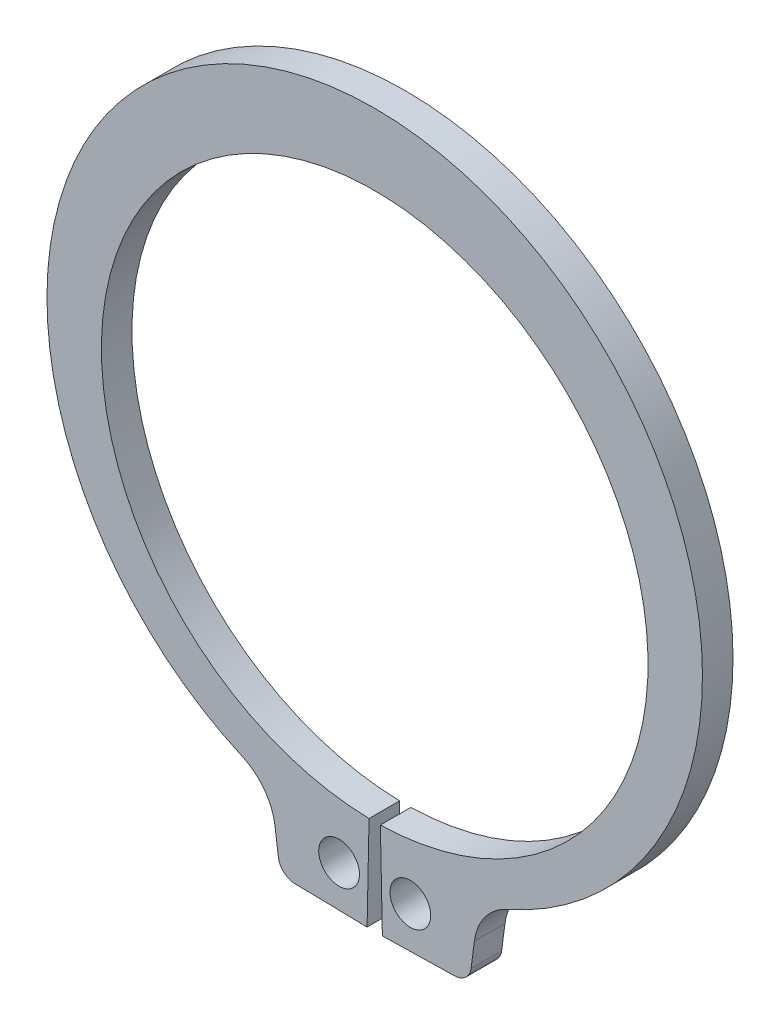
SolidWorks part; units mm, degrees
ref_plane "Plane1" through (0, 0, 0) normal (0, 0, 1) x (1, 0, 0)
ref_plane "Plane2" through (0, 0, 0) normal (0, 1, 0) x (1, 0, 0)
ref_plane "Plane3" through (0, 0, 0) normal (1, 0, 0) x (0, 0, -1)
sketch "Clipboard" plane through (0, 0, 0) normal (0, 0, 1) x (1, 0, 0)
  line L0 (0, 0) -> (2.1, 0)
  line L1 (0, 0) -> (0, 1.15)
  line L2 (0, 0) -> (0, -2.8)
  circle A0 centre (0, 0) radius 0.6
  circle A1 centre (0, 0) radius 8.5
  dimension "HoleDia" = 1.2
  dimension "ShaftDia" = 17
  dimension "LargeSection" = 2.1
  dimension "SmallSection" = 1.15
  dimension "LugSection" = 2.8
sketch "BodySke" plane through (0, 0, 0) normal (0, 0, 1) x (1, 0, 0)
  line L0 (-1.5431, 0) -> (1.5431, 0) construction
  line L1 (0, 0) -> (0, 10.15) construction
  line L2 (0.1669, -8.0483) -> (0.225, -10.8477)
  line L3 (-0.1669, -8.0483) -> (-0.225, -10.8477)
  line L4 (0, 0) -> (4.572, -9.8397) construction
  line L5 (0, 0) -> (-4.572, -9.8397) construction
  line L6 (0.225, -10.8477) -> (2.353, -10.8035)
  line L7 (2.9364, -9.6244) -> (2.8384, -10.3689)
  line L8 (-2.9364, -9.6244) -> (-2.8384, -10.3689)
  line L9 (-0.225, -10.8477) -> (-2.353, -10.8035)
  circle A0 centre (0, 0) radius 8.05 construction
  arc A1 (0.1669, -8.0483) -> (-0.1669, -8.0483) centre (0, 0) ccw
  arc A2 (3.8767, -8.3433) -> (-3.8767, -8.3433) centre (0, 0.497) ccw construction
  arc A3 (0.225, -10.8477) -> (2.717, -10.5043) centre (0, 0) ccw construction
  arc A4 (3.9047, -8.331) -> (2.9364, -9.6244) centre (4.572, -9.8397) ccw
  arc A5 (-2.9364, -9.6244) -> (-3.9047, -8.331) centre (-4.572, -9.8397) ccw
  arc A6 (-2.717, -10.5043) -> (-0.225, -10.8477) centre (0, 0) ccw construction
  arc A7 (3.9047, -8.331) -> (-3.9047, -8.331) centre (0, 0.497) ccw
  arc A8 (-2.9922, -9.2007) -> (2.9922, -9.2007) centre (0, 0) ccw construction
  circle A9 centre (1.05, -9.6179) radius 0.6
  circle A10 centre (-1.05, -9.6179) radius 0.6
  arc A11 (2.8384, -10.3689) -> (2.353, -10.8035) centre (2.3427, -10.3036) cw
  arc A12 (-2.8384, -10.3689) -> (-2.353, -10.8035) centre (-2.3427, -10.3036) ccw
  point P28 (2.8243, -10.476)
  point P31 (-2.8243, -10.476)
  dimension "GrooveDia" = 16.1
  dimension "LugRad" = 10.85
  dimension "HoleOffsetRad" = 9.675
  dimension "HoleDia" = 1.2
  dimension "D3" = 0.5
  dimension "LargeRad" = 10.15
  dimension "SmallRad" = 9.2
  dimension "SmallAngle" = 49.843
  dimension "D2" = 15
  dimension "HoleSpacing" = 2.1
  dimension "Gap" = 0.45
extrude "Body" add sketch "BodySke" against normal blind 0.9
sketch "NotSke" plane through (0, 0, 0) normal (0, 0, 1) x (1, 0, 0)
  line L0 (1.05, -9.0179) -> (1.05, -10.2179)
  line L1 (1.05, -10.2179) -> (-1.05, -10.2179)
  line L2 (-1.05, -10.2179) -> (-1.05, -9.0179)
  line L3 (-1.05, -9.0179) -> (1.05, -9.0179)
  circle A0 centre (1.05, -9.6179) radius 0.6 construction
  circle A1 centre (-1.05, -9.6179) radius 0.6 construction
extrude "Notch" [suppressed] cut sketch "NotSke" against normal through all
equation "' \"ShaftDia@Clipboard\" = 4"
equation "' \"Thickness@Body\" = 0.25"
equation "' \"GrooveDia@BodySke\" = 3.8"
equation "' \"LugSection@Clipboard\" = 1.35"
equation "' \"LargeSection@Clipboard\" = 0.65"
equation "' \"SmallSection@Clipboard\" = 0.4"
equation "' \"HoleDia@Clipboard\" = 0.6"
equation "' \"ShaftDia@Clipboard\" = 15"
equation "' \"Thickness@Body\" = 0.9"
equation "' \"GrooveDia@BodySke\" = 14.15"
equation "' \"LugSection@Clipboard\" = 2.8"
equation "' \"LargeSection@Clipboard\" = 1.8"
equation "' \"SmallSection@Clipboard\" = 1.05"
equation "' \"HoleDia@Clipboard\" = 1.2"
equation "\"Gap@BodySke\" =  \"Thickness@Body\" / 2"
equation "\"LargeRad@BodySke\" =  \"GrooveDia@BodySke\" / 2 +  \"LargeSection@Clipboard\""
equation "\"SmallRad@BodySke\" =  \"GrooveDia@BodySke\" / 2 +  \"SmallSection@Clipboard\""
equation "\"LugRad@BodySke\" = \"GrooveDia@BodySke\" / 2 + \"LugSection@Clipboard\""
equation "\"HoleOffsetRad@BodySke\" = (  \"ShaftDia@Clipboard\" / 2 + \"LugRad@BodySke\" ) / 2"
equation "\"HoleSpacing@BodySke\" = \"Gap@BodySke\"  * 2 +  \"HoleDia@Clipboard\""
equation "\"HoleDia@BodySke\" =  \"HoleDia@Clipboard\""
equation "\"SmallAngle@BodySke\" = atn(\"HoleSpacing@BodySke\" / 2 / sqr(\"HoleOffsetRad@BodySke\"  * \"HoleOffsetRad@BodySke\" - (\"HoleSpacing@BodySke\" / 2) * (\"HoleSpacing@BodySke\" / 2) ))  * 8 * ( 180 / 3.141593)"
